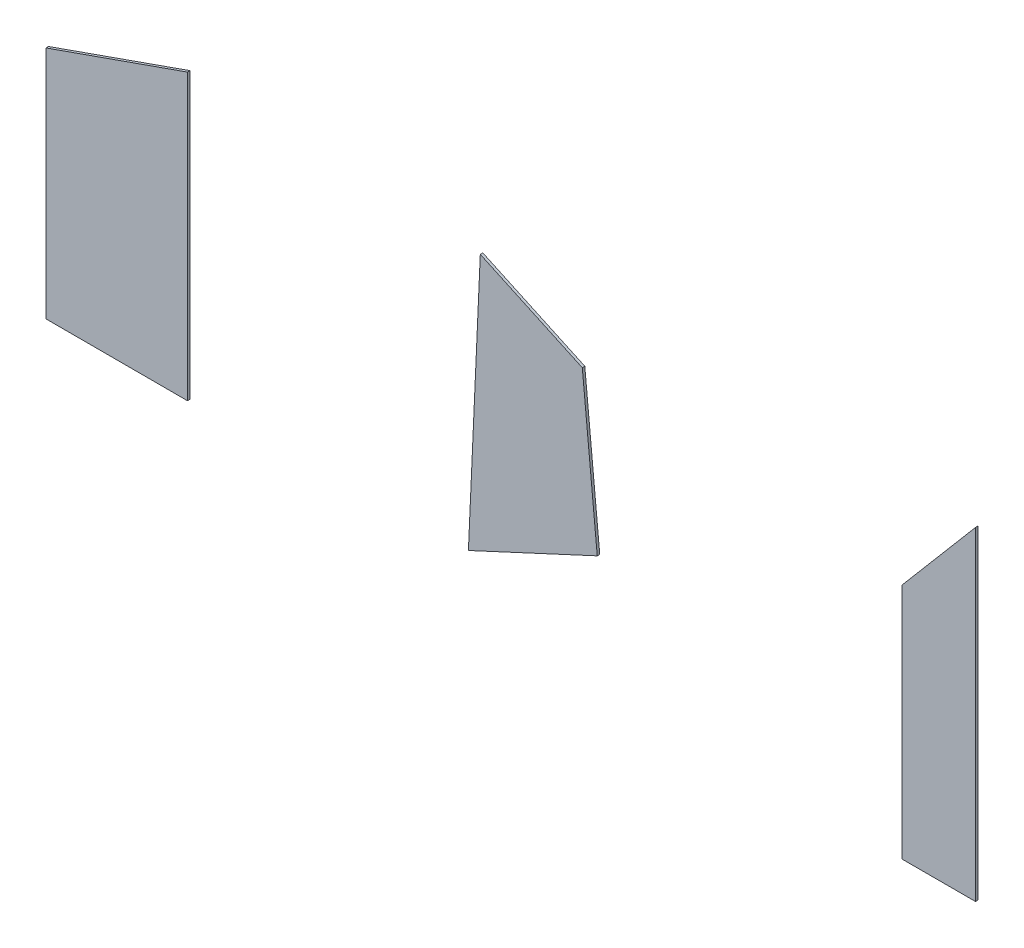
SolidWorks part; units mm, degrees
ref_plane "Ön Düzlem" through (0, 0, 0) normal (0, 0, 1) x (1, 0, 0)
ref_plane "Üst Düzlem" through (0, 0, 0) normal (0, 1, 0) x (1, 0, 0)
ref_plane "Sağ Düzlem" through (0, 0, 0) normal (1, 0, 0) x (0, 0, -1)
sketch "Çizim1" plane through (0, 0, 0) normal (0, 0, 1) x (1, 0, 0)
  line L0 (-11544.7634, -24265.1755) -> (-11544.7757, -25628.8354)
  line L1 (-12222.547, -25628.1544) -> (-12222.5268, -24503.9058)
  line L2 (-12222.547, -25628.1544) -> (-11544.7757, -25628.8354)
  line L3 (-11544.7634, -24265.1755) -> (-12222.5268, -24503.9058)
  line L4 (-8121.5663, -24681.8322) -> (-8121.5945, -25818.8235)
  line L5 (-10141.8989, -24320.0242) -> (-10198.8763, -25577.1605)
  line L6 (-9653.2509, -24545.8474) -> (-10141.8989, -24320.0242)
  line L7 (-9653.2509, -24545.8474) -> (-9581.6923, -25290.8506)
  line L8 (-10198.8763, -25577.1605) -> (-9581.6923, -25290.8506)
  line L9 (-7769.5607, -24266.9091) -> (-8121.5663, -24681.8322)
  line L10 (-7769.5607, -24266.9091) -> (-7769.6136, -25818.845)
  line L11 (-7769.6136, -25818.845) -> (-8121.5945, -25818.8235)
  point P0 (0, 0)
  dimension "D1" = 1363.6599
  dimension "D2" = 677.7713
  dimension "D3" = 1124.2487
  dimension "D4" = 238.7303
  dimension "D5" = 677.7633
  dimension "D6" = 56.9774
  dimension "D7" = 488.648
  dimension "D8" = 1257.1363
  dimension "D9" = 617.184
  dimension "D10" = 286.3099
  dimension "D11" = 745.0032
  dimension "D12" = 71.5586
  dimension "D13" = 225.8232
  dimension "D14" = 1136.9913
  dimension "D15" = 1551.9359
  dimension "D16" = 351.9808
  dimension "D17" = 414.9231
  dimension "D18" = 352.0056
extrude "Yükseklik-Ekstrüzyon1" add sketch "Çizim1" along normal blind 12
